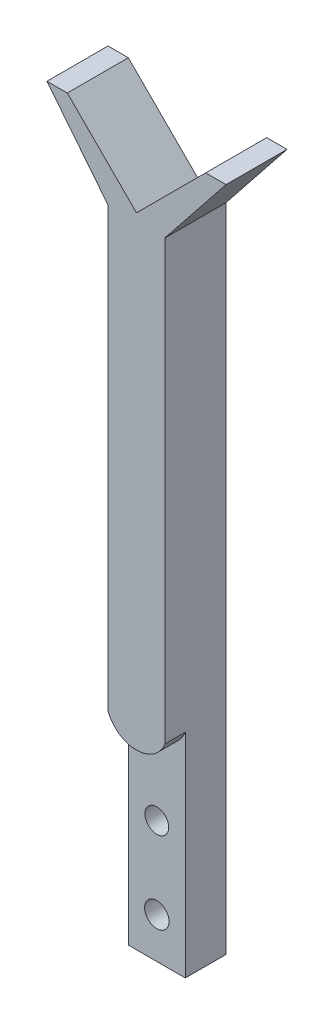
SolidWorks part; units mm, degrees
ref_plane "Front Plane" through (0, 0, 0) normal (0, 0, 1) x (1, 0, 0)
ref_plane "Top Plane" through (0, 0, 0) normal (0, 1, 0) x (1, 0, 0)
ref_plane "Right Plane" through (0, 0, 0) normal (1, 0, 0) x (0, 0, -1)
sketch "Sketch1" plane through (0, 0, 0) normal (0, 0, 1) x (1, 0, 0)
  line L0 (7, -2.83) -> (22, 16)
  line L2 (-7, -2.83) -> (-7, -162.83)
  line L3 (-7, -162.83) -> (7, -162.83)
  line L4 (7, -2.83) -> (7, -162.83)
  line L5 (22, 16) -> (17, 16)
  line L6 (17, 16) -> (0, -1)
  line L7 (0, -1) -> (-17, 16)
  line L8 (-17, 16) -> (-22, 16)
  line L9 (-22, 16) -> (-7, -2.83)
  line L10 (0, -162.83) -> (0, -7.6723) construction
  line L11 (0, 0) -> (-39.5424, 0) construction
  point P11 (0, -162.83)
  point P13 (0, 0)
  point P14 (0, 0)
  dimension "D1" = 45
  dimension "D2" = 1
  dimension "D3" = 2.83
  dimension "D4" = 5
  dimension "D5" = 14
  dimension "D6" = 16
  dimension "D7" = 160
extrude "Boss-Extrude1" add sketch "Sketch1" along normal blind 15
sketch "Sketch2" plane through (0, 0, 15) normal (0, 0, 1) x (1, 0, 0)
  line L0 (0, -132.83) -> (0, -152.83) construction
  line L1 (0, -152.83) -> (0, -162.83) construction
  line L2 (-7, -162.83) -> (7, -162.83) construction
  circle A0 centre (0, -132.83) radius 2.925
  circle A1 centre (0, -152.83) radius 3
  dimension "D1" = 5.85
  dimension "D2" = 6
  dimension "D3" = 10
  dimension "D4" = 20
extrude "Cut-Extrude1" cut sketch "Sketch2" against normal through all
sketch "Sketch3" plane through (0, 0, 15) normal (0, 0, 1) x (1, 0, 0)
  line L0 (-7, -110.5226) -> (-7, -162.83)
  line L1 (-7, -2.83) -> (-7, -162.83) construction
  line L2 (-7, -162.83) -> (7, -162.83)
  line L3 (7, -162.83) -> (7, -110.5226)
  line L4 (7, -162.83) -> (7, -2.83) construction
  arc A1 (-7, -110.5226) -> (7, -110.5226) centre (0, -107.83) ccw
  dimension "D1" = 7.5
  dimension "D2" = 55
extrude "Cut-Extrude2" cut sketch "Sketch3" against normal blind 5
